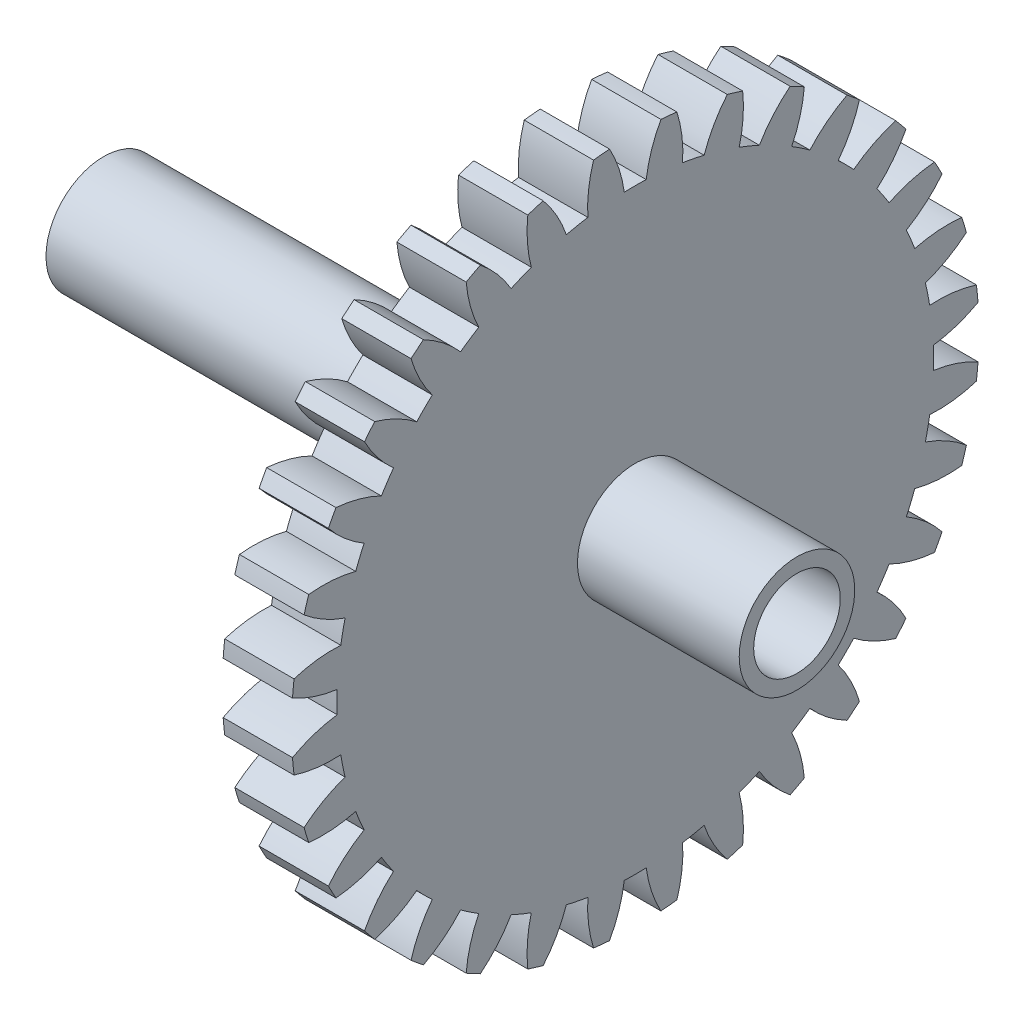
SolidWorks part; units mm, degrees
ref_plane "Plane1" through (0, 0, 0) normal (0, 0, 1) x (1, 0, 0)
ref_plane "Plane2" through (0, 0, 0) normal (0, 1, 0) x (1, 0, 0)
ref_plane "Plane3" through (0, 0, 0) normal (1, 0, 0) x (0, 0, -1)
sketch "HoldingSke" plane through (0, 0, 0) normal (0, 1, 0) x (1, 0, 0)
  line L0 (0, 0) -> (0.4846, -0.3028)
  line L1 (-15, 0) -> (100, 0) construction
  line L2 (0, 0) -> (-2.1039, 2.3779)
  line L3 (0, 0) -> (-11.863, 4.5341)
  line L4 (0, 0) -> (7.3237, 4.5764)
  line L5 (0, 0) -> (-46.8476, -17.4728)
  line L6 (0, 0) -> (-4.9738, -3.3558)
  line L7 (-2.1039, 2.3779) -> (8.6586, 51.2059)
  line L8 (-76.2, 54.61) -> (-76.1, 54.61)
  line L9 (-67.7845, 28.3722) -> (-49.3413, 33.142)
  line L10 (-76.2, 71.12) -> (104.1128, 71.12)
  line L11 (0, 0) -> (-6, 0)
  line L12 (-76.2, 101.6) -> (-76.147, 101.6)
  line L13 (24.9733, 27.94) -> (52.9518, 28.4284)
  line L14 (24.9733, 27.94) -> (24.9743, 27.94)
  line L15 (24.9733, 27.94) -> (100.4006, 29.5858)
  line L16 (-63.627, -1.75) -> (-12.827, -1.75)
  circle A0 centre (0, 0) radius 0.4
  circle A1 centre (0, 0) radius 25.8115
  circle A2 centre (0, 0) radius 37.5
  circle A3 centre (0, 0) radius 0.4
  dimension "MHD" = 51.623
  dimension "Hub_dia" = 75
  dimension "Bore" = 0.8
  dimension "MBD" = 0.8
  dimension "Num_teeth" = 32
  dimension "Pitch" = 0.5714
  dimension "Overall_len" = 50
  dimension "Show_teeth" = 32
  dimension "Thickness" = 6
  dimension "OAL" = 50.0001
  dimension "T_dim" = 0.1
  dimension "Ap" = 14.5
  dimension "H" = 19.05
  dimension "Pitch_radius" = 180.3128
  dimension "Width" = 6
  dimension "Backlash" = 0.053
  dimension "Addendum_fac" = 1
  dimension "Dedendum_fac" = 1.25
  dimension "Clearance_fac" = 0.25
  dimension "Dedendum_add" = 0.001
  dimension "Module" = 1.75
sketch "BasProSke" plane through (0, 0, 0) normal (0, 1, 0) x (1, 0, 0)
  line L0 (-10, 0) -> (60, 0) construction
  line L1 (0, 0) -> (0, 29.75)
  line L2 (0, 0) -> (6, 0)
  line L3 (6, 0) -> (6, 29.75)
  line L4 (6, 29.75) -> (0, 29.75)
  dimension "Thickness" = 6
  dimension "Diameter" = 59.5
revolve "Base-Revolve" add sketch "BasProSke" angle 360 about L0
sketch "TooCutSke" plane through (0, 0, 0) normal (1, 0, 0) x (0, 0, -1)
  line L1 (0, 0) -> (0, 107) construction
  line L2 (0, 0) -> (-1.4666, 27.9616) construction
  line L3 (0, 0) -> (-5.4832, 55.672) construction
  line L4 (-1.4666, 27.9616) -> (-2.7416, 27.836) construction
  arc A0 (0.9481, 25.7941) -> (-0.9481, 25.7941) centre (0, 0) ccw
  arc A1 (2.2372, 29.6912) -> (-2.2372, 29.6912) centre (0, 0) ccw
  circle A2 centre (0, 0) radius 28 construction
  circle A3 centre (0, 0) radius 27.1081 construction
  arc A4 (-0.9481, 25.7941) -> (-2.2372, 29.6912) centre (-12.0459, 24.2847) ccw
  arc A5 (2.2372, 29.6912) -> (0.9481, 25.7941) centre (12.0459, 24.2847) ccw
  dimension "Root_dia" = 51.623
  dimension "Overcut_dia" = 59.5508
  dimension "Pitch_dia" = 56
  dimension "Base_dia" = 54.2163
  dimension "Flank_rad" = 11.2
  dimension "Half_ang" = 5.625
  dimension "Half_CT" = 1.2811
extrude "ToothCut" cut sketch "TooCutSke" along normal through all
fillet "Breaks" [suppressed] radius 0.035
fillet "RootFillets" [suppressed] radius 0.4385
pattern_circular "TeethCuts" count 32 every 11.25 about axis through (-10, 0, 0) along (1, 0, 0) of "ToothCut", "RootFillets", "Breaks"
sketch "HubNeaOneSke" plane through (0, 0, 0) normal (-1, 0, 0) x (0, 0, 1)
  circle A0 centre (0, 0) radius 25.8115
  dimension "Diameter" = 51.623
extrude "HubNearOne" [suppressed] add sketch "HubNeaOneSke" along normal blind 44.0001
sketch "HubNeaBotSke" plane through (0, 0, 0) normal (-1, 0, 0) x (0, 0, 1)
  circle A0 centre (0, 0) radius 25.8115
  dimension "Diameter" = 51.623
extrude "HubNearBoth" [suppressed] add sketch "HubNeaBotSke" along normal blind 22
ref_plane "FarPln" through (6, 0, 0) normal (1, 0, 0) x (0, 0, -1)
sketch "HubFarSke" plane through (6, 0, 0) normal (1, 0, 0) x (0, 0, -1)
  circle A0 centre (0, 0) radius 25.8115
  dimension "Diameter" = 51.623
extrude "HubFar" [suppressed] add sketch "HubFarSke" along normal blind 22
sketch "BorSke" plane through (0, 0, 0) normal (1, 0, 0) x (0, 0, -1)
  circle A0 centre (0, 0) radius 0.4
  dimension "Diameter" = 0.8
extrude "Bore" cut sketch "BorSke" along normal mid plane 100.0001
sketch "KeySke" plane through (0, 0, 0) normal (1, 0, 0) x (0, 0, -1)
  line L0 (-0.05, 0) -> (-0.05, 0.5)
  line L1 (-0.05, 0.5) -> (0.05, 0.5)
  line L2 (0.05, 0.5) -> (0.05, 0)
  line L3 (0, 0) -> (0, 34) construction
  line L4 (-0.05, 0) -> (0.05, 0)
  dimension "Offset" = 0.5
  dimension "Width" = 0.1
extrude "Keyway" [suppressed] cut sketch "KeySke" along normal mid plane 100.0001
pattern_circular "Keyway2" [suppressed] count 2 every 90 about axis through (-10, 0, 0) along (1, 0, 0)
sketch "Sketch1" plane through (0, 0, 0) normal (-1, 0, 0) x (0, 0, 1)
  circle A0 centre (0, 0) radius 5
  circle A1 centre (0, 0) radius 3.75
  dimension "D1" = 10
  dimension "D2" = 7.5
extrude "Boss-Extrude1" add sketch "Sketch1" along normal blind 40 and the other way blind 20
sketch "Sketch2" plane through (0, 0, 0) normal (-1, 0, 0) x (0, 0, 1)
  circle A0 centre (0, 0) radius 3.75
  dimension "D1" = 7.5
extrude "Cut-Extrude1" cut sketch "Sketch2" against normal blind 10
sketch "Sketch3" plane through (0, 0, 0) normal (-1, 0, 0) x (0, 0, 1)
  line L1 (0, 0) -> (-63.6911, 6.5639) construction
  circle A0 centre (-24.2714, 2.5014) radius 1.725
  dimension "D1" = 3.45
  dimension "D2" = 24.4
extrude "Cut-Extrude2" cut sketch "Sketch3" against normal blind 2.5
equation "' \"Module@HoldingSke\" = 6.35"
equation "' \"Num_teeth@HoldingSke\" = 12"
equation "' \"Ap@HoldingSke\" =  20"
equation "' \"Ap@HoldingSke\" = 20"
equation "' \"Width@HoldingSke\" = 0.5 * 25.4"
equation "' \"Hub_dia@HoldingSke\"= 1 * 25.4"
equation "' \"Hub_dia@HoldingSke\" = 1 * 25.4"
equation "' \"Overall_len@HoldingSke\" = 1.0 * 25.4"
equation "' \"Bore@HoldingSke\" = 0.75 * 25.4"
equation "' \"T_dim@HoldingSke\" = 0.1 * 25.4"
equation "' \"Width@KeySke\" = 0.25 * 25.4"
equation "' \"Show_teeth@HoldingSke\" = 13"
equation "' \"Backlash@HoldingSke\" = 0.009 * 25.4"
equation "' \"Addendum_fac@HoldingSke\" = 1.0"
equation "' \"Dedendum_fac@HoldingSke\" = 1.25"
equation "' \"Dedendum_add@HoldingSke\" = 0.00005 * 25.4"
equation "' \"Clearance_fac@HoldingSke\" = 0.25"
equation "\"Pitch@HoldingSke\" = 1 / \"Module@HoldingSke\""
equation "\"Overcut_dia@TooCutSke\" = (\"Num_teeth@HoldingSke\" + 2 * \"Addendum_fac@HoldingSke\") / \"Pitch@HoldingSke\" + 0.002 * 25.4"
equation "\"Pitch_dia@TooCutSke\" = \"Num_teeth@HoldingSke\" / \"Pitch@HoldingSke\""
equation "\"Base_dia@TooCutSke\" = \"Num_teeth@HoldingSke\" / \"Pitch@HoldingSke\" * cos((\"Ap@HoldingSke\"  * 3.14159265 / 180))"
equation "\"Root_dia@TooCutSke\" = (\"Num_teeth@HoldingSke\" + 2) / \"Pitch@HoldingSke\" - 2 * (\"Addendum_fac@HoldingSke\" + \"Dedendum_fac@HoldingSke\") / \"Pitch@HoldingSke\" - \"Dedendum_add@HoldingSke\" * 2"
equation "\"Half_ang@TooCutSke\" = 180 / \"Num_teeth@HoldingSke\""
equation "\"Half_CT@TooCutSke\" = \"Num_teeth@HoldingSke\" / \"Pitch@HoldingSke\" * sin((3.14159265 / 2 / \"Num_teeth@HoldingSke\")) / 2 - 7 * \"Backlash@HoldingSke\" / 4"
equation "\"Flank_rad@TooCutSke\" = \"Num_teeth@HoldingSke\" / \"Pitch@HoldingSke\" / 5"
equation "\"Radius@RootFillets\" = \"Clearance_fac@HoldingSke\" / \"Pitch@HoldingSke\" + \"Dedendum_add@HoldingSke\""
equation "\"Break_rad@Breaks\" = 0.02 / \"Pitch@HoldingSke\""
equation "\"Thickness@HoldingSke\" = \"Width@HoldingSke\""
equation "\"OAL@HoldingSke\" = \"Thickness@HoldingSke\""
equation "\"MHD@HoldingSke\" = (\"Num_teeth@HoldingSke\" + 2) / \"Pitch@HoldingSke\" - 2 * (\"Addendum_fac@HoldingSke\" + \"Dedendum_fac@HoldingSke\")  / \"Pitch@HoldingSke\" - \"Dedendum_add@HoldingSke\" * 2"
equation "\"MBD@HoldingSke\" = (\"Num_teeth@HoldingSke\" + 2) / \"Pitch@HoldingSke\" - 2 * (\"Addendum_fac@HoldingSke\" + \"Dedendum_fac@HoldingSke\")  / \"Pitch@HoldingSke\" - \"Dedendum_add@HoldingSke\" * 2 - 0.002 * 25.4"
equation "\"MHD@HoldingSke\" = ((sgn( \"MHD@HoldingSke\" - \"Hub_dia@HoldingSke\" )-1)*( \"MHD@HoldingSke\" - \"Hub_dia@HoldingSke\" ))/-2+ \"Hub_dia@HoldingSke\""
equation "\"MBD@HoldingSke\" = ((sgn( \"MBD@HoldingSke\" - \"Bore@HoldingSke\" )-1)*( \"MBD@HoldingSke\" - \"Bore@HoldingSke\" ))/-2+ \"Bore@HoldingSke\""
equation "\"OAL@HoldingSke\" = ((sgn( \"OAL@HoldingSke\" - \"Overall_len@HoldingSke\" )+1)*( \"OAL@HoldingSke\" - \"Overall_len@HoldingSke\" ))/2 + \"Overall_len@HoldingSke\" + 0.000002 * 25.4"
equation "\"Num_teeth@TeethCuts\" = int( \"Show_teeth@HoldingSke\" ) + 1"
equation "\"Num_teeth@TeethCuts\" = ((sgn( \"Num_teeth@TeethCuts\" - \"Num_teeth@HoldingSke\" )-1)*( \"Num_teeth@TeethCuts\" - \"Num_teeth@HoldingSke\" ))/-2+ \"Num_teeth@HoldingSke\""
equation "\"Num_teeth@TeethCuts\" = ((sgn( \"Num_teeth@TeethCuts\" - 2.0)+1)*( \"Num_teeth@TeethCuts\" - 2.0))/2 +2.0"
equation "\"Angle@TeethCuts\" = 360.0 / \"Num_teeth@HoldingSke\""
equation "\"Diameter@BasProSke\" = (\"Num_teeth@HoldingSke\" + 2 * \"Addendum_fac@HoldingSke\") / \"Pitch@HoldingSke\""
equation "\"Thickness@BasProSke\"  = \"Thickness@HoldingSke\""
equation "' \"Fillet_rad@BasProSke\" =  \"Thickness@HoldingSke\" * 0.05"
equation "' \"Fillet_rad@BasProSke\" = \"Thickness@HoldingSke\" * 0.05"
equation "\"MHD@HoldingSke\" = ((sgn( \"MHD@HoldingSke\" - \"Root_dia@TooCutSke\" )-1)*( \"MHD@HoldingSke\" - \"Root_dia@TooCutSke\" ))/-2+ \"Root_dia@TooCutSke\""
equation "\"Diameter@HubNeaOneSke\" = \"MHD@HoldingSke\""
equation "\"Length@HubNearOne\" = \"OAL@HoldingSke\" - \"Thickness@BasProSke\""
equation "\"Diameter@HubNeaBotSke\" = \"MHD@HoldingSke\""
equation "\"Length@HubNearBoth\" = ( \"OAL@HoldingSke\" - \"Thickness@BasProSke\" ) / 2.0"
equation "\"Thickness@FarPln\" = \"Thickness@BasProSke\""
equation "\"Diameter@HubFarSke\" = \"MHD@HoldingSke\""
equation "\"Length@HubFar\" = ( \"OAL@HoldingSke\" - \"Thickness@BasProSke\" ) / 2.0"
equation "\"Diameter@BorSke\" = \"MBD@HoldingSke\""
equation "\"D1@Bore\" = \"OAL@HoldingSke\" * 2.0"
equation "\"D1@Keyway\" = \"OAL@HoldingSke\" * 2.0"
equation "\"Offset@KeySke\" = \"T_dim@HoldingSke\" + \"MBD@HoldingSke\" / 2.0"
